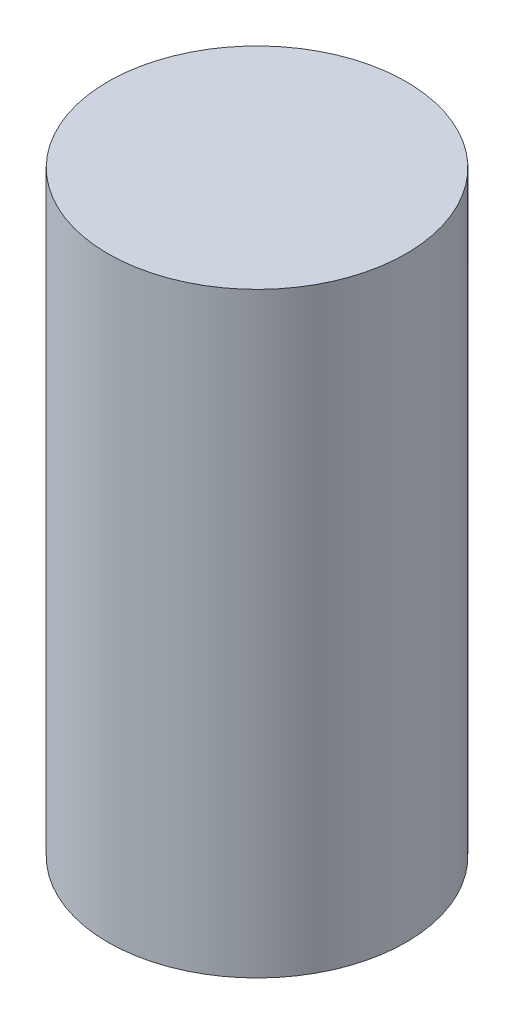
SolidWorks part; units mm, degrees
ref_plane "Front Plane" through (0, 0, 0) normal (0, 0, 1) x (1, 0, 0)
ref_plane "Top Plane" through (0, 0, 0) normal (0, 1, 0) x (1, 0, 0)
ref_plane "Right Plane" through (0, 0, 0) normal (1, 0, 0) x (0, 0, -1)
sketch "Sketch1" plane through (0, 0, 0) normal (0, 1, 0) x (1, 0, 0)
  circle A0 centre (0, 0) radius 9.525
  dimension "D1" = 19.05
extrude "Boss-Extrude1" add sketch "Sketch1" along normal blind 38.1
